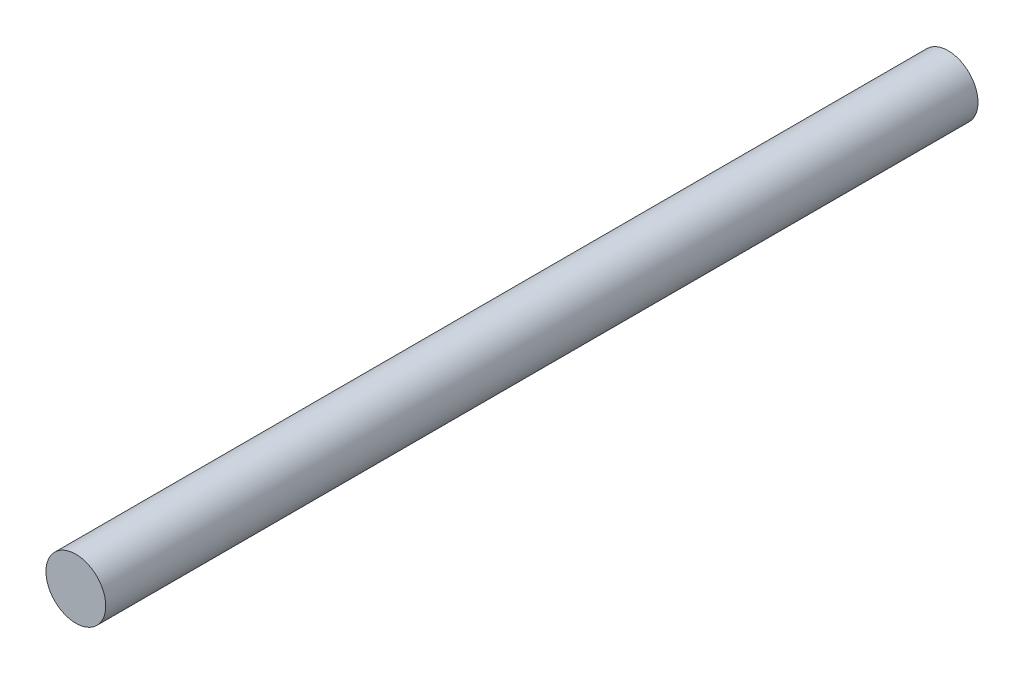
SolidWorks part; units mm, degrees
ref_plane "前基準面" through (0, 0, 0) normal (0, 0, 1) x (1, 0, 0)
ref_plane "上基準面" through (0, 0, 0) normal (0, 1, 0) x (1, 0, 0)
ref_plane "右基準面" through (0, 0, 0) normal (1, 0, 0) x (0, 0, -1)
sketch "草圖1" plane through (0, 0, 0) normal (0, 0, 1) x (1, 0, 0)
  circle A0 centre (0, 0) radius 6
  dimension "D1" = 12
extrude "填料-伸長1" add sketch "草圖1" along normal blind 175
